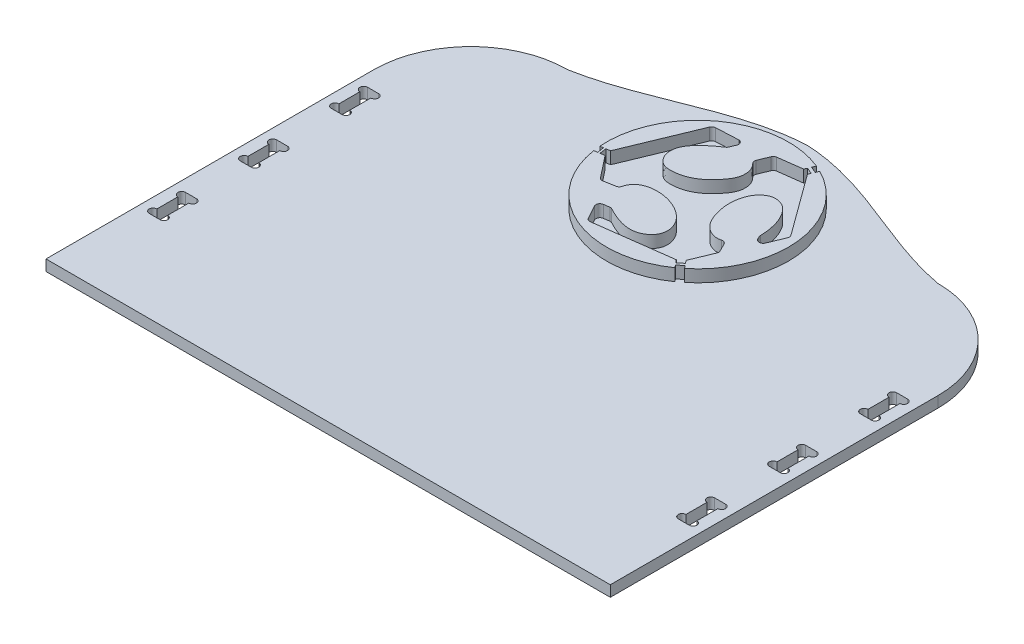
SolidWorks part; units mm, degrees
ref_plane "Front Plane" through (0, 0, 0) normal (0, 0, 1) x (1, 0, 0)
ref_plane "Top Plane" through (0, 0, 0) normal (0, 1, 0) x (1, 0, 0)
ref_plane "Right Plane" through (0, 0, 0) normal (1, 0, 0) x (0, 0, -1)
sketch "Sketch3" plane through (0, 0, 0) normal (0, 1, 0) x (1, 0, 0)
  line L0 (-910, 0) -> (-910, 600) construction
  line L1 (0, 0) -> (-930, 0)
  line L2 (0, 0) -> (0, 540)
  line L3 (-160, 700) -> (-770, 700)
  line L4 (-930, 0) -> (-930, 540)
  line L5 (-465, 0) -> (-465, 700) construction
  line L6 (-20, 150) -> (-38, 150)
  line L7 (-910, 450) -> (-892, 450)
  line L8 (-910, 462.7) -> (-910, 497.3)
  line L9 (-910, 510) -> (-892, 510)
  line L10 (-892, 462.7) -> (-892, 497.3)
  line L11 (-910, 300) -> (-892, 300)
  line L12 (-910, 312.7) -> (-910, 347.3)
  line L13 (-910, 360) -> (-892, 360)
  line L14 (-892, 312.7) -> (-892, 347.3)
  line L15 (-910, 150) -> (-892, 150)
  line L16 (-910, 162.7) -> (-910, 197.3)
  line L17 (-910, 210) -> (-892, 210)
  line L18 (-892, 162.7) -> (-892, 197.3)
  line L19 (-38, 162.7) -> (-38, 197.3)
  line L20 (-20, 210) -> (-38, 210)
  line L21 (-20, 162.7) -> (-20, 197.3)
  line L22 (-38, 312.7) -> (-38, 347.3)
  line L23 (-20, 312.7) -> (-20, 347.3)
  line L24 (-20, 360) -> (-38, 360)
  line L25 (-20, 450) -> (-38, 450)
  line L26 (-20, 510) -> (-38, 510)
  line L27 (-20, 462.7) -> (-20, 497.3)
  line L28 (-38, 462.7) -> (-38, 497.3)
  line L29 (-38, 300) -> (-20, 300)
  arc A0 (0, 540) -> (-160, 700) centre (-160, 540) ccw
  arc A1 (-770, 700) -> (-930, 540) centre (-770, 540) ccw
  arc A2 (-892, 497.3) -> (-892, 510) centre (-892, 503.65) ccw
  arc A3 (-910, 510) -> (-910, 497.3) centre (-910, 503.65) ccw
  arc A4 (-892, 450) -> (-892, 462.7) centre (-892, 456.35) ccw
  arc A5 (-910, 462.7) -> (-910, 450) centre (-910, 456.35) ccw
  arc A6 (-892, 347.3) -> (-892, 360) centre (-892, 353.65) ccw
  arc A7 (-910, 360) -> (-910, 347.3) centre (-910, 353.65) ccw
  arc A8 (-892, 300) -> (-892, 312.7) centre (-892, 306.35) ccw
  arc A9 (-910, 312.7) -> (-910, 300) centre (-910, 306.35) ccw
  arc A10 (-910, 210) -> (-910, 197.3) centre (-910, 203.65) ccw
  arc A11 (-892, 197.3) -> (-892, 210) centre (-892, 203.65) ccw
  arc A12 (-892, 150) -> (-892, 162.7) centre (-892, 156.35) ccw
  arc A13 (-910, 162.7) -> (-910, 150) centre (-910, 156.35) ccw
  arc A14 (-20, 162.7) -> (-20, 150) centre (-20, 156.35) cw
  arc A15 (-38, 150) -> (-38, 162.7) centre (-38, 156.35) cw
  arc A16 (-38, 197.3) -> (-38, 210) centre (-38, 203.65) cw
  arc A17 (-20, 210) -> (-20, 197.3) centre (-20, 203.65) cw
  arc A18 (-20, 312.7) -> (-20, 300) centre (-20, 306.35) cw
  arc A19 (-38, 300) -> (-38, 312.7) centre (-38, 306.35) cw
  arc A20 (-38, 347.3) -> (-38, 360) centre (-38, 353.65) cw
  arc A21 (-20, 360) -> (-20, 347.3) centre (-20, 353.65) cw
  arc A22 (-20, 462.7) -> (-20, 450) centre (-20, 456.35) cw
  arc A23 (-38, 450) -> (-38, 462.7) centre (-38, 456.35) cw
  arc A24 (-38, 497.3) -> (-38, 510) centre (-38, 503.65) cw
  arc A25 (-20, 510) -> (-20, 497.3) centre (-20, 503.65) cw
  spline S0 degree 3 poles (-770, 700) (-664.6964, 719.0846) (-573.9965, 783.952) (-465, 789.5092) knots 0 0 0 0 1 1 1 1
  spline S1 degree 3 poles (-160, 700) (-265.3036, 719.0846) (-356.0035, 783.952) (-465, 789.5092) knots 0 0 0 0 1 1 1 1
  point P7 (0, 700)
  point P10 (-930, 700)
  point P15 (-910, 150)
  point P16 (-910, 300)
  point P17 (-910, 450)
  dimension "D3" = 160
  dimension "D14" = 12.7
  dimension "D15" = 12.7
  dimension "D16" = 12.7
  dimension "D17" = 12.7
  dimension "D18" = 12.7
  dimension "D19" = 12.7
  dimension "D20" = 12.7
  dimension "D21" = 12.7
  dimension "D22" = 12.7
  dimension "D23" = 12.7
  dimension "D24" = 12.7
  dimension "D25" = 12.7
  dimension "D1" = 930
  dimension "D2" = 700
  dimension "D4" = 450
  dimension "D5" = 150
  dimension "D6" = 300
  dimension "D7" = 20
  dimension "D8" = 18
  dimension "D9" = 18
  dimension "D10" = 18
  dimension "D11" = 60
  dimension "D12" = 60
  dimension "D13" = 60
  dimension "D26" = 510
  dimension "D27" = 34.6
  dimension "D28" = 34.6
  dimension "D29" = 34.6
  dimension "D30" = 210
  dimension "D31" = 360
extrude "Boss-Extrude1" add sketch "Sketch3" along normal blind 18
sketch "Sketch4" plane through (0, 18, 0) normal (0, 1, 0) x (1, 0, 0)
  line L1 (0, 0) -> (-930, 0) construction
  line L4 (-465, 0) -> (-465, 652.6854) construction
  point P0 (-465, 608.7705)
  line B0 (-379.2229, 485.7173) -> (-382.737, 490.0203)
  line B1 (-382.737, 490.0203) -> (-373.9535, 497.1872)
  line B2 (-373.9535, 497.1872) -> (-370.1702, 492.5504)
  line B3 (-397.4037, 742.6755) -> (-399.5952, 737.3714)
  line B4 (-399.5952, 737.3714) -> (-410.0778, 741.7024)
  line B5 (-410.0778, 741.7024) -> (-407.7224, 747.4034)
  line B6 (-614.5568, 597.2567) -> (-609.3054, 598.0636)
  line B7 (-609.3054, 598.0636) -> (-607.584, 586.8611)
  line B8 (-607.584, 586.8611) -> (-613.2593, 585.9891)
  line B9 (-605.9548, 598.5785) -> (-604.2334, 587.376)
  line B10 (-599.1745, 599.6203) -> (-605.9548, 598.5785)
  line B11 (-551.489, 715.0368) -> (-599.1745, 599.6203)
  line B12 (-509.5267, 720.7768) -> (-545.7446, 719.0769)
  line B13 (-507.0254, 702.4012) -> (-503.1684, 711.7363)
  line B14 (-458.3964, 723.4031) -> (-465.5795, 706.0174)
  line B15 (-413.8532, 732.5646) -> (-453.1981, 727.3946)
  line B16 (-412.0106, 737.0244) -> (-413.8532, 732.5646)
  line B17 (-401.5279, 732.6934) -> (-412.0106, 737.0244)
  line B18 (-403.3706, 728.2336) -> (-401.5279, 732.6934)
  line B19 (-329.9314, 627.6371) -> (-403.3706, 728.2336)
  line B20 (-339.9065, 595.2859) -> (-329.1683, 621.2763)
  line B21 (-353.9623, 599.0441) -> (-351.7833, 594.7972)
  line B22 (-365.8817, 546.8593) -> (-372.6994, 560.1469)
  line B23 (-380.5635, 505.2881) -> (-365.6558, 541.3701)
  line B24 (-376.7314, 500.5916) -> (-380.5635, 505.2881)
  line B25 (-385.5132, 493.4197) -> (-376.7314, 500.5916)
  line B26 (-389.4517, 498.2424) -> (-385.5132, 493.4197)
  line B27 (-514.5488, 481.6208) -> (-389.4517, 498.2424)
  line B28 (-533.5383, 507.5325) -> (-521.1511, 484.9611)
  line B29 (-519.3212, 518.414) -> (-528.6607, 517.1731)
  line B30 (-562.5478, 550.2302) -> (-544.0122, 553.5243)
  line B31 (-597.0293, 588.483) -> (-568.8406, 552.6298)
  line B32 (-604.2334, 587.376) -> (-597.0293, 588.483)
  arc B33 (-370.1702, 492.5504) -> (-397.4037, 742.6755) centre (-465, 608.7705) ccw
  arc B34 (-407.7224, 747.4034) -> (-614.5568, 597.2567) centre (-465, 608.7705) ccw
  arc B35 (-613.2593, 585.9891) -> (-379.2229, 485.7173) centre (-465, 608.7705) ccw
  arc B36 (-545.7446, 719.0769) -> (-551.489, 715.0368) centre (-545.4377, 712.5366) ccw
  arc B37 (-503.1684, 711.7363) -> (-509.5267, 720.7768) centre (-509.2198, 714.2365) ccw
  arc B38 (-509.3759, 699.5001) -> (-507.0254, 702.4012) centre (-513.0767, 704.9014) ccw
  arc B39 (-465.5795, 706.0174) -> (-463.933, 698.6729) centre (-459.5282, 703.5172) ccw
  arc B40 (-453.1981, 727.3946) -> (-458.3964, 723.4031) centre (-452.3451, 720.9029) ccw
  arc B41 (-329.1683, 621.2763) -> (-329.9314, 627.6371) centre (-335.2197, 623.7765) ccw
  arc B42 (-351.7833, 594.7972) -> (-339.9065, 595.2859) centre (-345.9578, 597.7861) ccw
  arc B43 (-354.6804, 601.8058) -> (-353.9623, 599.0441) centre (-348.1369, 602.033) ccw
  arc B44 (-372.6994, 560.1469) -> (-380.2918, 563.4625) centre (-378.5249, 557.158) ccw
  arc B45 (-365.6558, 541.3701) -> (-365.8817, 546.8593) centre (-371.7072, 543.8703) ccw
  arc B46 (-521.1511, 484.9611) -> (-514.5488, 481.6208) centre (-515.4112, 488.1112) ccw
  arc B47 (-528.6607, 517.1731) -> (-533.5383, 507.5325) centre (-527.7984, 510.6826) ccw
  arc B48 (-515.3968, 517.7109) -> (-519.3212, 518.414) centre (-518.4588, 511.9236) ccw
  arc B49 (-544.0122, 553.5243) -> (-538.8132, 558.3536) centre (-545.1579, 559.9708) ccw
  arc B50 (-568.8406, 552.6298) -> (-562.5478, 550.2302) centre (-563.6934, 556.6766) ccw
  spline B51 degree 3 poles (-463.933, 698.6729) (-456.3169, 691.7478) (-451.4537, 670.8479) (-468.1281, 647.707) (-487.4091, 628.7235) (-512.029, 620.5958) (-535.731, 620.7538) (-548.4945, 635.5517) (-553.6784, 668.7263) (-523.4963, 689.8251) (-509.3759, 699.5001) knots 0.010514 0.010514 0.010514 0.010514 0.140441 0.245215 0.361326 0.482761 0.571283 0.64375 0.712105 0.981384 0.981384 0.981384 0.981384
  spline B52 degree 3 poles (-380.2918, 563.4625) (-389.6214, 560.8478) (-407.3403, 567.4876) (-419.8451, 588.0393) (-426.3643, 610.176) (-426.7539, 634.5727) (-418.3743, 656.5998) (-401.3858, 668.8656) (-379.8566, 666.1375) (-359.4658, 641.7586) (-355.2282, 617.5791) (-354.6804, 601.8058) knots 0.006193 0.006193 0.006193 0.006193 0.129362 0.215047 0.307703 0.422373 0.521839 0.59763 0.671661 0.775788 0.978099 0.978099 0.978099 0.978099
  spline B53 degree 3 poles (-538.8132, 558.3536) (-534.2975, 576.0703) (-503.0191, 584.7198) (-464.6858, 573.1136) (-440.0442, 551.3618) (-435.3722, 522.8011) (-465.2991, 494.1666) (-498.6237, 508.8365) (-515.3968, 517.7109) knots 0.009911 0.009911 0.009911 0.009911 0.210711 0.384963 0.51568 0.617717 0.718634 0.985505 0.985505 0.985505 0.985505
sketch_block_instance "Fab-Logo-Block1-1"
sketch_block "Fab-Logo-Block1"
extrude "Boss-Extrude3" add sketch "Sketch4" along normal blind 20
